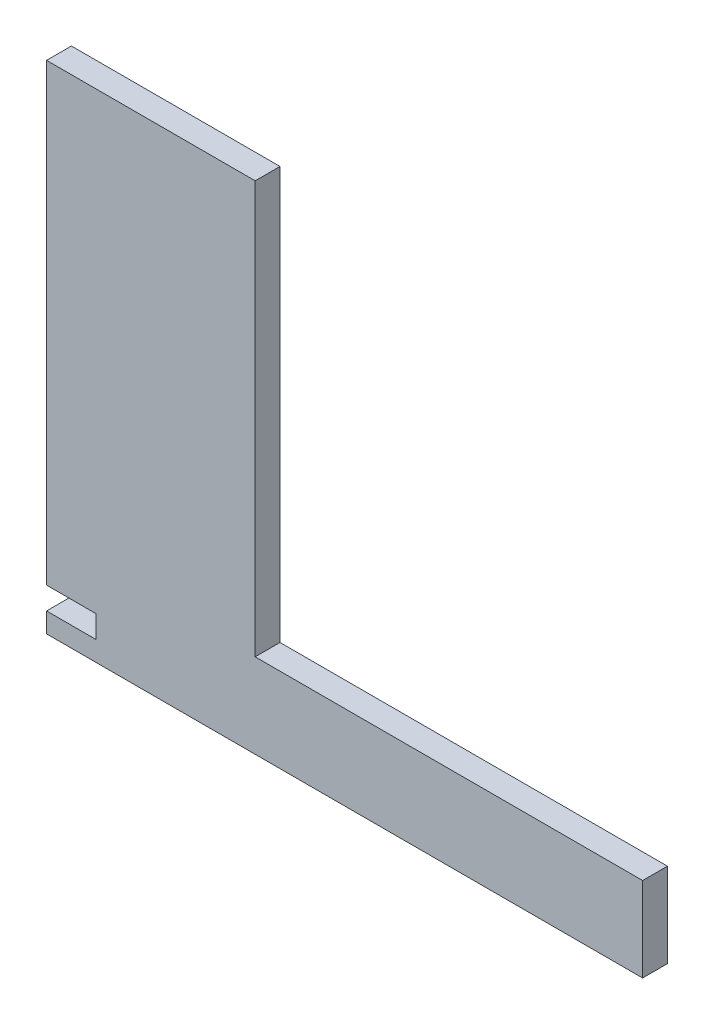
SolidWorks part; units mm, degrees
ref_plane "Ebene vorne" through (0, 0, 0) normal (0, 0, 1) x (1, 0, 0)
ref_plane "Ebene oben" through (0, 0, 0) normal (0, 1, 0) x (1, 0, 0)
ref_plane "Ebene rechts" through (0, 0, 0) normal (1, 0, 0) x (0, 0, -1)
sketch "Skizze1" plane through (0, 0, 0) normal (0, 0, 1) x (1, 0, 0)
  line L0 (-9.1089, 5.5297) -> (-9.1089, 1.0297)
  line L1 (-9.1089, 1.0297) -> (-19.1089, 1.0297)
  line L2 (-19.1089, 1.0297) -> (-19.1089, -2.9703)
  line L3 (-19.1089, -2.9703) -> (100.8911, -2.9703)
  line L4 (100.8911, -2.9703) -> (100.8911, 14.0297)
  line L5 (100.8911, 14.0297) -> (22.8911, 14.0297)
  line L6 (22.8911, 14.0297) -> (22.8911, 97.0297)
  line L7 (22.8911, 97.0297) -> (-19.1089, 97.0297)
  line L8 (-19.1089, 97.0297) -> (-19.1089, 5.5297)
  line L9 (-19.1089, 5.5297) -> (-9.1089, 5.5297)
  dimension "D1" = 4
  dimension "D2" = 4.5
  dimension "D3" = 10
  dimension "D4" = 17
  dimension "D5" = 42
  dimension "D6" = 120
  dimension "D7" = 91.5
extrude "Aufsatz-Linear austragen1" add sketch "Skizze1" along normal blind 5
